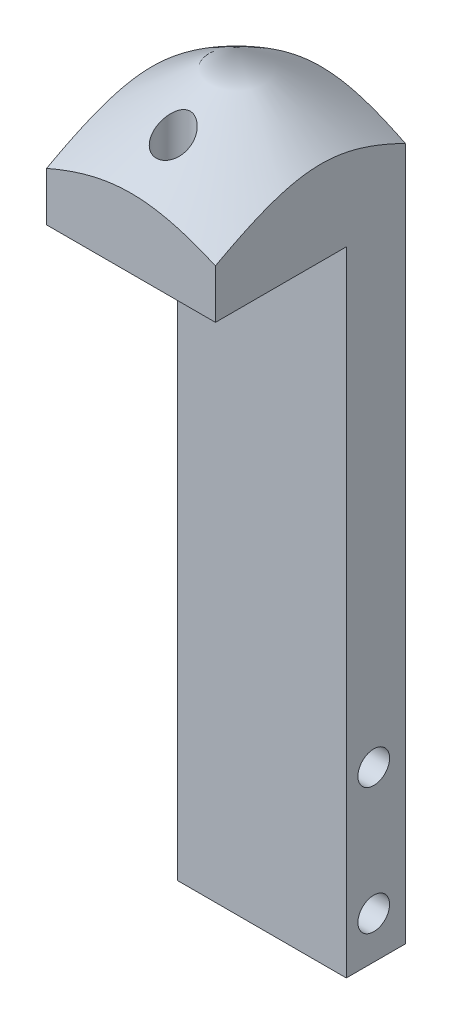
SolidWorks part; units mm, degrees
material "6061-T6 (SS)"
ref_plane "Front Plane" through (0, 0, 0) normal (0, 0, 1) x (1, 0, 0)
ref_plane "Top Plane" through (0, 0, 0) normal (0, 1, 0) x (1, 0, 0)
ref_plane "Right Plane" through (0, 0, 0) normal (1, 0, 0) x (0, 0, -1)
sketch "Sketch1" plane through (0, 0, 0) normal (1, 0, 0) x (0, 0, -1)
  line L0 (8.89, -95.25) -> (8.89, 22.225)
  line L1 (8.89, 22.225) -> (-19.685, 22.225)
  line L2 (-19.685, 22.225) -> (-19.685, 0)
  line L3 (-19.685, 0) -> (0, 0)
  line L4 (0, 0) -> (0, -95.25)
  line L5 (0, -95.25) -> (8.89, -95.25)
  line L6 (-26.6971, 5.5669) -> (-3.81, 21.5926) construction
  line L7 (-3.81, 21.5926) -> (19.0771, 5.5669) construction
  point P2 (0, 0)
  point P5 (0, 0)
  point P11 (0, 0)
  point P13 (8.89, 12.7)
  dimension "D1" = 8.89
  dimension "D2" = 28.575
  dimension "D3" = 95.25
  dimension "D4" = 110
  dimension "D5" = 27.94
  dimension "D6" = 12.7
  dimension "D7" = 22.225
  dimension "D8" = 12.7
extrude "Boss-Extrude1" add sketch "Sketch1" along normal mid plane 25.4
sketch "Sketch2" plane through (0, 0, 0) normal (1, 0, 0) x (0, 0, -1)
  line L4 (-3.81, 21.5926) -> (-3.81, 70.9395) construction
  line L5 (-26.6971, 5.5669) -> (-3.81, 21.5926) construction
  line L6 (-26.6971, 5.5669) -> (-3.81, 21.5926)
  line L8 (-26.6971, 22.225) -> (-26.6971, 5.5669)
  line L9 (-3.81, 21.5926) -> (-3.81, 22.225)
  line L10 (-3.81, 22.225) -> (-26.6971, 22.225)
  line L11 (8.89, 22.225) -> (-19.685, 22.225) construction
  point P2 (-32.4566, 95.7628)
  point P3 (0, 0)
revolve "Cut-Revolve4" cut sketch "Sketch2" angle 360 about L4
hole_wizard "1/4-20 Tapped Hole1" positions "Sketch5" profile "Sketch6" tap size "1/4-20" standard "ANSI Inch" end condition through all
sketch "Sketch5" plane through (0, 0, 0) normal (0, -1, 0) x (-1, 0, 0)
  line L1 (-12.7, 8.89) -> (12.7, 8.89) construction
  point P0 (0, -13.335)
  dimension "D1" = 22.225
cosmetic thread "Hole Thread2"
sketch "Sketch6" plane through (0, 0, 13.335) normal (1, 0, 0) x (0, 0, -1)
  line L0 (0, 0) -> (0, 21.5926)
  line L1 (0, 21.5926) -> (2.5527, 21.5926)
  line L2 (2.5527, 21.5926) -> (2.5527, 0)
  line L5 (2.5527, 0) -> (0, 0)
  line L11 (0, -6.35) -> (0, 107.95) construction
  dimension "Thru Tap Drill Dia." = 5.1054
  dimension "Thru Tap Drill Depth" = 21.5926
hole_wizard "3/16 (0.1875) Dowel Hole1" positions "Sketch7" profile "Sketch8" hole size "3/16" standard "ANSI Inch" end condition through all
sketch "Sketch7" plane through (12.7, 0, 0) normal (1, 0, 0) x (0, 0, -1)
  line L0 (0, -95.25) -> (8.89, -95.25) construction
  line L4 (8.89, -95.25) -> (8.89, 9.0165) construction
  point P0 (4.1275, -88.9)
  point P2 (4.1275, -69.85)
  dimension "D1" = 25.4
  dimension "D2" = 6.35
  dimension "D3" = 4.7625
sketch "Sketch8" plane through (12.7, -88.9, -4.1275) normal (0, 1, 0) x (0, 0, -1)
  line L0 (0, 0) -> (0, 25.4)
  line L1 (0, 25.4) -> (2.3812, 25.4)
  line L2 (2.3812, 25.4) -> (2.3812, 0)
  line L5 (2.3812, 0) -> (0, 0)
  line L11 (0, -6.35) -> (0, 107.95) construction
  dimension "Thru Hole Dia." = 4.7625
  dimension "Thru Hole Depth" = 25.4
